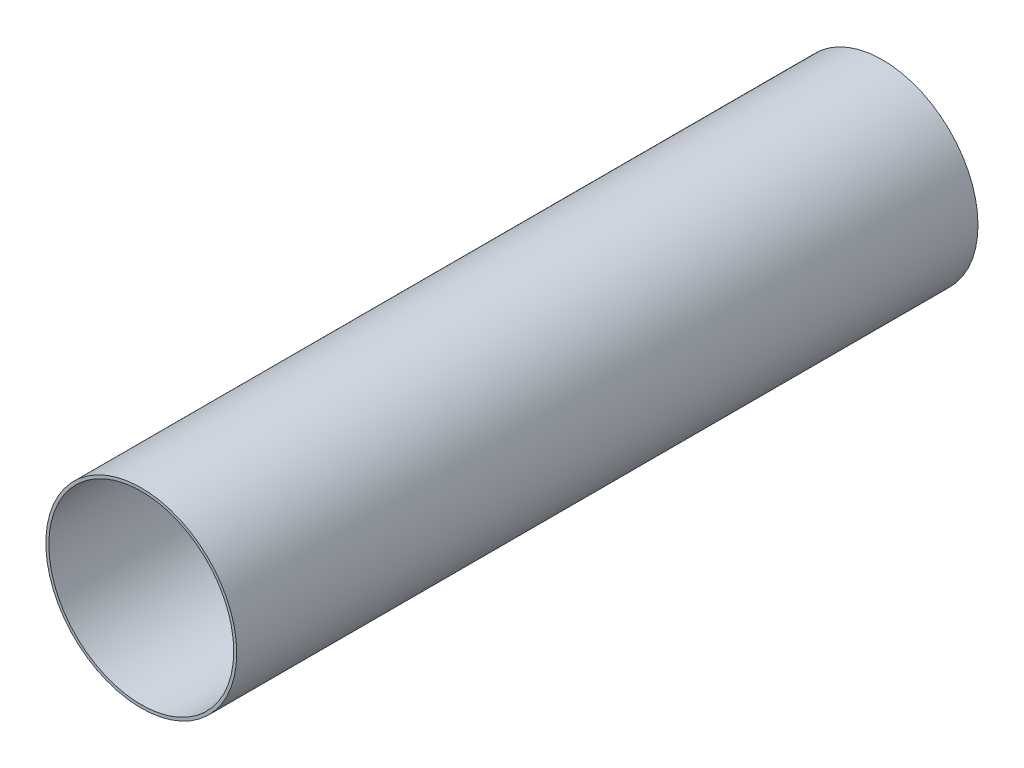
SolidWorks part; units mm, degrees
ref_plane "Front Plane" through (0, 0, 0) normal (0, 0, 1) x (1, 0, 0)
ref_plane "Top Plane" through (0, 0, 0) normal (0, 1, 0) x (1, 0, 0)
ref_plane "Right Plane" through (0, 0, 0) normal (1, 0, 0) x (0, 0, -1)
sketch "Sketch1" plane through (0, 0, 0) normal (0, 0, 1) x (1, 0, 0)
  circle A0 centre (0, 0) radius 65.405
  circle A1 centre (0, 0) radius 63.373
  dimension "D1" = 126.746
  dimension "D2" = 130.81
extrude "Boss-Extrude1" add sketch "Sketch1" along normal mid plane 508
equation "\"AIRFRAME_OD\"= 5.15in"
equation "\"AIRFRAME_ID\"= 4.99in"
equation "\"FLAT_T\"= 0.125in"
equation "\"NOSE_EXP_L\"= 27in"
equation "\"NOSE_SHOULDER_L\"= 5in"
equation "\"MAIN_L\"= 30in"
equation "\"RECO_COUP_L\"= 10in"
equation "\"RECO_SWITCH_L\"= 2in"
equation "\"DROGUE_L\"= 20in"
equation "\"ATS_FORE_COUP_L\"= 5.5in"
equation "\"ATS_AFT_COUP_L\"= 4.5in"
equation "\"LOWER_L\"= 30in"
equation "\"FIN_N\"= 4"
equation "\"CR_AFT_X\"= 0.5in"
equation "\"CR_FORE_X\"= 9.25in"
equation "\"D1@Sketch1\"=\"AIRFRAME_ID\""
equation "\"D2@Sketch1\"=\"AIRFRAME_OD\""
equation "\"D1@Boss-Extrude1\"=\"DROGUE_L\""
equation "\"FIN_ROOT\"= 8in"
equation "\"FIN_X\"= 0.75in"
equation "\"MOTOR_OD\"= 3.091in"
equation "\"MOTOR_ID\"= 3.00in"
equation "\"COUPLER_OD\"= 4.998in"
equation "\"COUPLER_ID\"= 4.85in"
equation "\"RECO_ROD_X\"= 3.5in"
equation "\"ATS_ROD_X\"= 3.75in"
equation "\"MOTOR_L\"= 14in"
equation "\"MOTOR_LOWER_X\"= 2in"
